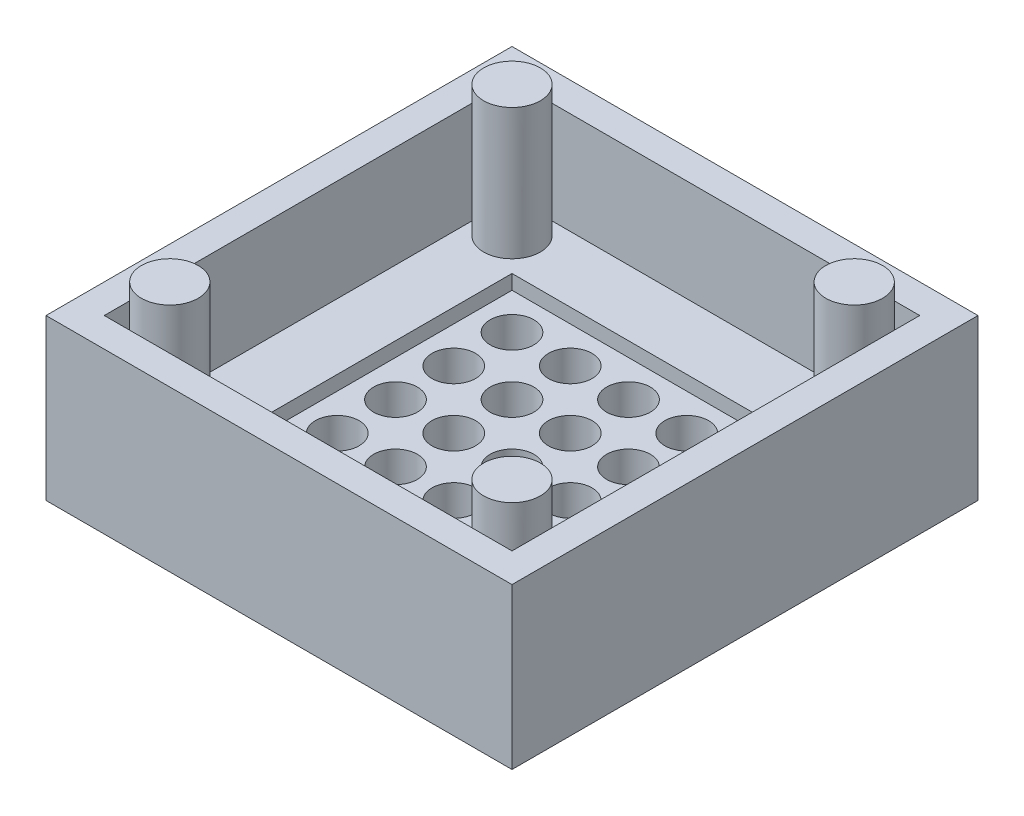
SolidWorks part; units mm, degrees
ref_plane "Front Plane" through (0, 0, 0) normal (0, 0, 1) x (1, 0, 0)
ref_plane "Top Plane" through (0, 0, 0) normal (0, 1, 0) x (1, 0, 0)
ref_plane "Right Plane" through (0, 0, 0) normal (1, 0, 0) x (0, 0, -1)
sketch "Sketch1" plane through (0, 0, 0) normal (0, 1, 0) x (1, 0, 0)
  line L1 (-16, -16) -> (16, -16)
  line L2 (-16, -16) -> (-16, 16)
  line L3 (-16, 16) -> (16, 16)
  line L4 (16, -16) -> (16, 16)
  line L5 (-16, -16) -> (16, 16) construction
  line L6 (-16, 16) -> (16, -16) construction
  point P0 (0, 0)
  dimension "D1" = 32
extrude "Boss-Extrude1" add sketch "Sketch1" along normal blind 11
sketch "Sketch2" plane through (0, 11, 0) normal (0, 1, 0) x (1, 0, 0)
  line L0 (-16, -16) -> (16, -16) construction
  line L1 (-14, -14) -> (14, -14)
  line L2 (-14, -14) -> (-14, 14)
  line L3 (-14, 14) -> (14, 14)
  line L4 (14, -14) -> (14, 14)
  line L5 (-14, -14) -> (14, 14) construction
  line L6 (-14, 14) -> (14, -14) construction
  point P0 (0, 0)
  dimension "D1" = 2
extrude "Cut-Extrude1" cut sketch "Sketch2" against normal blind 7
sketch "Sketch3" plane through (0, 4, 0) normal (0, 1, 0) x (1, 0, 0)
  line L1 (-9.5, -9.5) -> (9.5, -9.5)
  line L2 (-9.5, -9.5) -> (-9.5, 9.5)
  line L3 (-9.5, 9.5) -> (9.5, 9.5)
  line L4 (9.5, -9.5) -> (9.5, 9.5)
  line L5 (-9.5, -9.5) -> (9.5, 9.5) construction
  line L6 (-9.5, 9.5) -> (9.5, -9.5) construction
  point P0 (0, 0)
  dimension "D1" = 19
extrude "Cut-Extrude2" cut sketch "Sketch3" against normal blind 1.5
sketch "Sketch4" plane through (0, 2.5, 0) normal (0, 1, 0) x (1, 0, 0)
  line L0 (-9.5, -9.5) -> (9.5, -9.5) construction
  line L1 (-8.5, -8.5) -> (8.5, -8.5)
  line L2 (-8.5, -8.5) -> (-8.5, 8.5)
  line L3 (-8.5, 8.5) -> (8.5, 8.5)
  line L4 (8.5, -8.5) -> (8.5, 8.5)
  line L5 (-8.5, -8.5) -> (8.5, 8.5) construction
  line L6 (-8.5, 8.5) -> (8.5, -8.5) construction
  point P0 (0, 0)
  dimension "D1" = 1
extrude "Boss-Extrude2" add sketch "Sketch4" along normal blind 1.5
sketch "Sketch6" plane through (0, 4, 0) normal (0, 1, 0) x (1, 0, 0)
  line L0 (-9.5, 9.5) -> (-14, 14) construction
  line L1 (0, 14) -> (0, -14) construction
  line L2 (14, 14) -> (-14, 14) construction
  line L3 (-14, -14) -> (14, -14) construction
  line L4 (-14, 0) -> (14, 0) construction
  line L5 (-14, 14) -> (-14, -14) construction
  line L6 (14, -14) -> (14, 14) construction
  circle A0 centre (-11.75, 11.75) radius 1.95
  circle A1 centre (11.75, 11.75) radius 1.95
  circle A2 centre (11.75, -11.75) radius 1.95
  circle A3 centre (-11.75, -11.75) radius 1.95
  dimension "D1" = 3.9
extrude "Boss-Extrude3" add sketch "Sketch6" along normal blind 9
sketch "Sketch7" plane through (0, 4, 0) normal (0, 1, 0) x (1, 0, 0)
  line L0 (-6, 6) -> (6, -6) construction
  line L1 (6, -6) -> (6, 6) construction
  line L2 (6, 6) -> (-6, -6) construction
  circle A0 centre (-6, -6) radius 1.5
  circle A1 centre (-2, -6) radius 1.5
  circle A2 centre (2, -6) radius 1.5
  circle A3 centre (6, -6) radius 1.5
  circle A4 centre (-2, -2) radius 1.5
  circle A5 centre (2, -2) radius 1.5
  circle A6 centre (6, -2) radius 1.5
  circle A7 centre (-2, 2) radius 1.5
  circle A8 centre (2, 2) radius 1.5
  circle A9 centre (6, 2) radius 1.5
  circle A10 centre (-2, 6) radius 1.5
  circle A11 centre (2, 6) radius 1.5
  circle A12 centre (6, 6) radius 1.5
  circle A13 centre (-6, -2) radius 1.5
  circle A14 centre (-6, 2) radius 1.5
  circle A15 centre (-6, 6) radius 1.5
  point P2 (0, 0)
  dimension "D3" = 3
  dimension "D4" = 4
  dimension "D1" = 4
  dimension "D2" = 4
extrude "Cut-Extrude3" cut sketch "Sketch7" against normal blind 3
